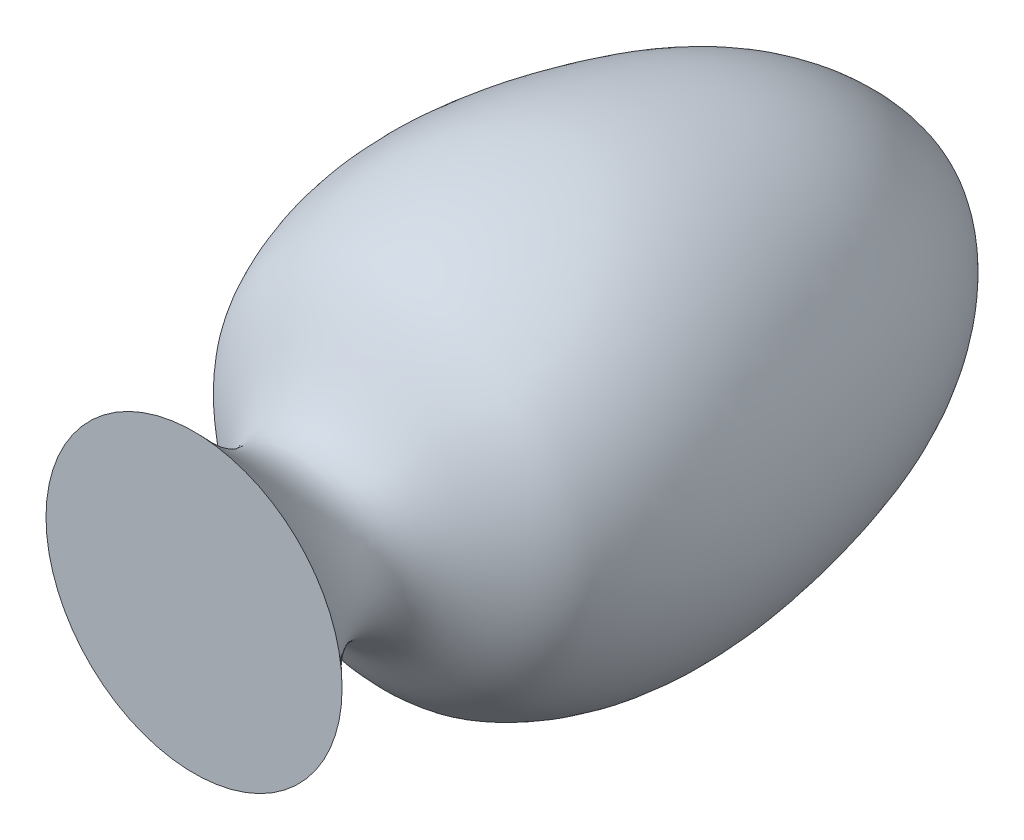
SolidWorks part; units mm, degrees
ref_plane "Front Plane" through (0, 0, 0) normal (0, 0, 1) x (1, 0, 0)
ref_plane "Top Plane" through (0, 0, 0) normal (0, 1, 0) x (1, 0, 0)
ref_plane "Right Plane" through (0, 0, 0) normal (1, 0, 0) x (0, 0, -1)
sketch "Sketch2" plane through (0, 0, 0) normal (0, 1, 0) x (1, 0, 0)
  line L2 (200, -1000) -> (0, -1000)
  line L7 (0, 0) -> (0, -1000)
  spline S0 degree 3 poles (0, 0) (101.5577, -26.8414) (214.3475, -143.9627) (294.4806, -403.7357) (311.5984, -603.8481) (198.7977, -815.1014) (-7.4055, -810.8394) (200, -1000) knots 0 0 0 0 0.252723 0.388743 0.700896 0.718239 1 1 1 1
  point P3 (0, 0)
  point P5 (256.9926, -705.6586)
  point P7 (173.2866, -118.0318)
  point P9 (219.3229, -190.5171)
  dimension "D2" = 1000
  dimension "D1" = 200
revolve "Revolve4" add sketch "Sketch2" angle 360 about L7
